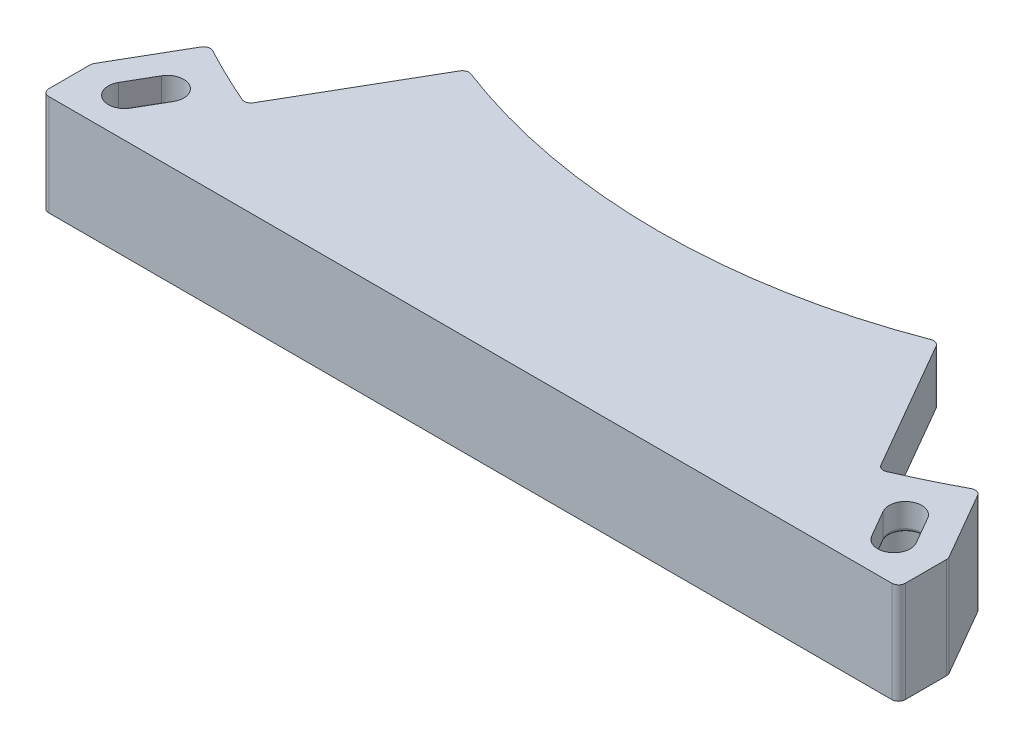
SolidWorks part; units mm, degrees
ref_plane "Front Plane" through (0, 0, 0) normal (0, 0, 1) x (1, 0, 0)
ref_plane "Top Plane" through (0, 0, 0) normal (0, 1, 0) x (1, 0, 0)
ref_plane "Right Plane" through (0, 0, 0) normal (1, 0, 0) x (0, 0, -1)
sketch "Sketch1" plane through (0, 0, 0) normal (0, 1, 0) x (1, 0, 0)
  line L0 (-57.2863, -105.4433) -> (-68, -124)
  line L1 (-68, -124) -> (68, -124)
  line L2 (68, -124) -> (57.2863, -105.4433)
  arc A1 (-57.2863, -105.4433) -> (57.2863, -105.4433) centre (0, 0) ccw
  dimension "D1" = 120
  dimension "D2" = 4
  dimension "D3" = 60
  dimension "D4" = 136
extrude "Boss-Extrude1" add sketch "Sketch1" along normal blind 15
sketch "Sketch2" plane through (0, 15, 0) normal (0, 1, 0) x (1, 0, 0)
  line L0 (-54.9043, -114.1675) -> (-57.2293, -118.1945) construction
  line L1 (-52.8042, -115.38) -> (-55.1292, -119.407)
  line L2 (-57.0044, -112.955) -> (-59.3294, -116.982)
  line L3 (-57.2863, -105.4433) -> (-68, -124) construction
  line L4 (0, -124) -> (0, -120) construction
  line L5 (-68, -124) -> (68, -124) construction
  line L6 (-54.9043, -114.1675) -> (-51.5525, -108.3621) construction
  line L7 (-57.2293, -118.1945) -> (-60.581, -124) construction
  line L8 (54.9043, -114.1675) -> (57.2293, -118.1945) construction
  line L9 (52.8042, -115.38) -> (55.1292, -119.407)
  line L10 (57.0044, -112.955) -> (59.3294, -116.982)
  arc A0 (-52.8042, -115.38) -> (-57.0044, -112.955) centre (-54.9043, -114.1675) ccw
  arc A1 (-59.3294, -116.982) -> (-55.1292, -119.407) centre (-57.2293, -118.1945) ccw
  arc A2 (-57.2863, -105.4433) -> (57.2863, -105.4433) centre (0, 0) ccw construction
  arc A3 (52.8042, -115.38) -> (57.0044, -112.955) centre (54.9043, -114.1675) cw
  arc A4 (59.3294, -116.982) -> (55.1292, -119.407) centre (57.2293, -118.1945) cw
  point P2 (-56.0668, -116.181)
  point P23 (56.0668, -116.181)
  dimension "D3" = 9.5
  dimension "D1" = 4.85
  dimension "D2" = 4
extrude "Cut-Extrude1" cut sketch "Sketch2" against normal through all
sketch "Sketch3" plane through (0, 15, 0) normal (0, 1, 0) x (1, 0, 0)
  line L0 (-54.9168, -114.1892) -> (-57.2168, -118.1729) construction
  line L1 (-51.0197, -116.4392) -> (-53.3197, -120.4229)
  line L2 (-58.8139, -111.9392) -> (-61.1139, -115.9229)
  line L3 (-58.1669, -114.9685) -> (-53.9667, -117.3935) construction
  line L4 (-57.2863, -105.4433) -> (-68, -124) construction
  line L5 (0, -120) -> (0, -124) construction
  line L6 (-68, -124) -> (68, -124) construction
  line L7 (-52.1697, -118.431) -> (-53.9667, -117.3935) construction
  line L8 (-55.1292, -119.407) -> (-52.8042, -115.38) construction
  line L9 (-59.9639, -113.931) -> (-58.1669, -114.9685) construction
  line L10 (-57.0044, -112.955) -> (-59.3294, -116.982) construction
  line L11 (54.9168, -114.1892) -> (57.2168, -118.1729) construction
  line L12 (51.0197, -116.4392) -> (53.3197, -120.4229)
  line L13 (58.8139, -111.9392) -> (61.1139, -115.9229)
  arc A0 (-51.0197, -116.4392) -> (-58.8139, -111.9392) centre (-54.9168, -114.1892) ccw
  arc A1 (-61.1139, -115.9229) -> (-53.3197, -120.4229) centre (-57.2168, -118.1729) ccw
  arc A2 (-57.2863, -105.4433) -> (57.2863, -105.4433) centre (0, 0) ccw construction
  arc A4 (51.0197, -116.4392) -> (58.8139, -111.9392) centre (54.9168, -114.1892) cw
  arc A5 (61.1139, -115.9229) -> (53.3197, -120.4229) centre (57.2168, -118.1729) cw
  point P2 (-56.0668, -116.181)
  point P26 (56.0668, -116.181)
  dimension "D2" = 13.6
  dimension "D1" = 9
extrude "Cut-Extrude3" cut sketch "Sketch3" against normal through all from offset 4 offset against normal yes
fillet "Fillet2" radius 0.5 16 edges at (58.4418, 11, 120.2947) (53.9667, 11, 117.3935) (53.6918, 11, 112.0674) (-53.6918, 11, 112.0674) (-58.1669, 11, 114.9685) (-58.4418, 11, 120.2947) (-52.1697, 11, 118.431) (-59.4668, 11, 122.07) (-59.9639, 11, 113.931) (59.4668, 11, 122.07) (52.1697, 11, 118.431) (52.6668, 11, 110.2921) (58.1669, 11, 114.9685) (-53.9667, 11, 117.3935) (-52.6668, 11, 110.2921) (59.9639, 11, 113.931)
sketch "Sketch4" plane through (0, 15, 0) normal (0, 1, 0) x (1, 0, 0)
  line L0 (0, -124) -> (0, -96) construction
  line L1 (-68, -124) -> (68, -124) construction
  line L14 (-35.0157, -89.3862) -> (-55, -124)
  line L15 (-68, -124) -> (68, -124) construction
  line L16 (-55, -124) -> (55, -124)
  line L17 (35.0157, -89.3862) -> (55, -124)
  line L18 (-57.2863, -105.4433) -> (-68, -124) construction
  arc A0 (-35.0157, -89.3862) -> (35.0157, -89.3862) centre (0, 0) ccw
  dimension "D1" = 110
  dimension "D3" = 28
extrude "Boss-Extrude2" add sketch "Sketch4" against normal blind 8
sketch "Sketch5" plane through (0, 7, 0) normal (0, -1, 0) x (1, 0, 0)
  line L0 (0, 96) -> (0, 120) construction
  line L1 (5.25, 102.75) -> (-5.25, 102.75)
  line L2 (5.25, 102.75) -> (5.25, 113.25)
  line L3 (5.25, 113.25) -> (-5.25, 113.25)
  line L4 (-5.25, 102.75) -> (-5.25, 113.25)
  line L5 (-5.25, 108) -> (5.25, 108) construction
  line L6 (17.9983, 101.2975) -> (20.3603, 111.5284)
  line L7 (28.2292, 98.9355) -> (17.9983, 101.2975)
  line L8 (28.2292, 98.9355) -> (30.5911, 109.1664)
  line L9 (30.5911, 109.1664) -> (20.3603, 111.5284)
  line L10 (-17.9983, 101.2975) -> (-20.3603, 111.5284)
  line L11 (-17.9983, 101.2975) -> (-28.2292, 98.9355)
  line L12 (-28.2292, 98.9355) -> (-30.5911, 109.1664)
  line L13 (-20.3603, 111.5284) -> (-30.5911, 109.1664)
  arc A0 (35.0157, 89.3862) -> (-35.0157, 89.3862) centre (0, 0) ccw construction
  arc A1 (47.1248, 110.3597) -> (-47.1248, 110.3597) centre (0, 0) ccw construction
  point P12 (0, 102.75)
  point P13 (0, 108)
  point P23 (0, 0)
  point P29 (0, 0)
  dimension "D1" = 10.5
  dimension "D2" = 10.5
  dimension "D5" = 13
  dimension "D6" = 13
  dimension "D3" = 2
  dimension "D4" = 2
extrude "Cut-Extrude4" cut sketch "Sketch5" against normal blind 7
sketch "Sketch6" plane through (0, 0, 0) normal (0, -1, 0) x (1, 0, 0)
  line L0 (63.7168, 116.5812) -> (63.7168, 124)
  line L1 (68, 124) -> (57.2863, 105.4433) construction
  line L2 (-68, 124) -> (68, 124) construction
  line L3 (63.7168, 124) -> (68, 124)
  line L4 (68, 124) -> (63.7168, 116.5812)
  line L5 (0, 120) -> (0, 124) construction
  line L6 (-68, 124) -> (-63.7168, 116.5812)
  line L7 (-63.7168, 124) -> (-68, 124)
  line L8 (-63.7168, 116.5812) -> (-63.7168, 124)
  arc A0 (57.2863, 105.4433) -> (-57.2863, 105.4433) centre (0, 0) ccw construction
  arc A2 (61.1139, 115.9229) -> (53.3197, 120.4229) centre (57.2168, 118.1729) ccw construction
  dimension "D1" = 2
extrude "Cut-Extrude5" cut sketch "Sketch6" against normal through all
fillet "Fillet1" radius 1 10 edges at (-57.2863, 7.5, 105.4433) (57.2863, 7.5, 105.4433) (47.1248, 11, 110.3597) (35.0157, 11, 89.3862) (-35.0157, 11, 89.3862) (-47.1248, 11, 110.3597) (-63.7168, 7.5, 124) (-63.7168, 7.5, 116.5812) (63.7168, 7.5, 124) (63.7168, 7.5, 116.5812)
